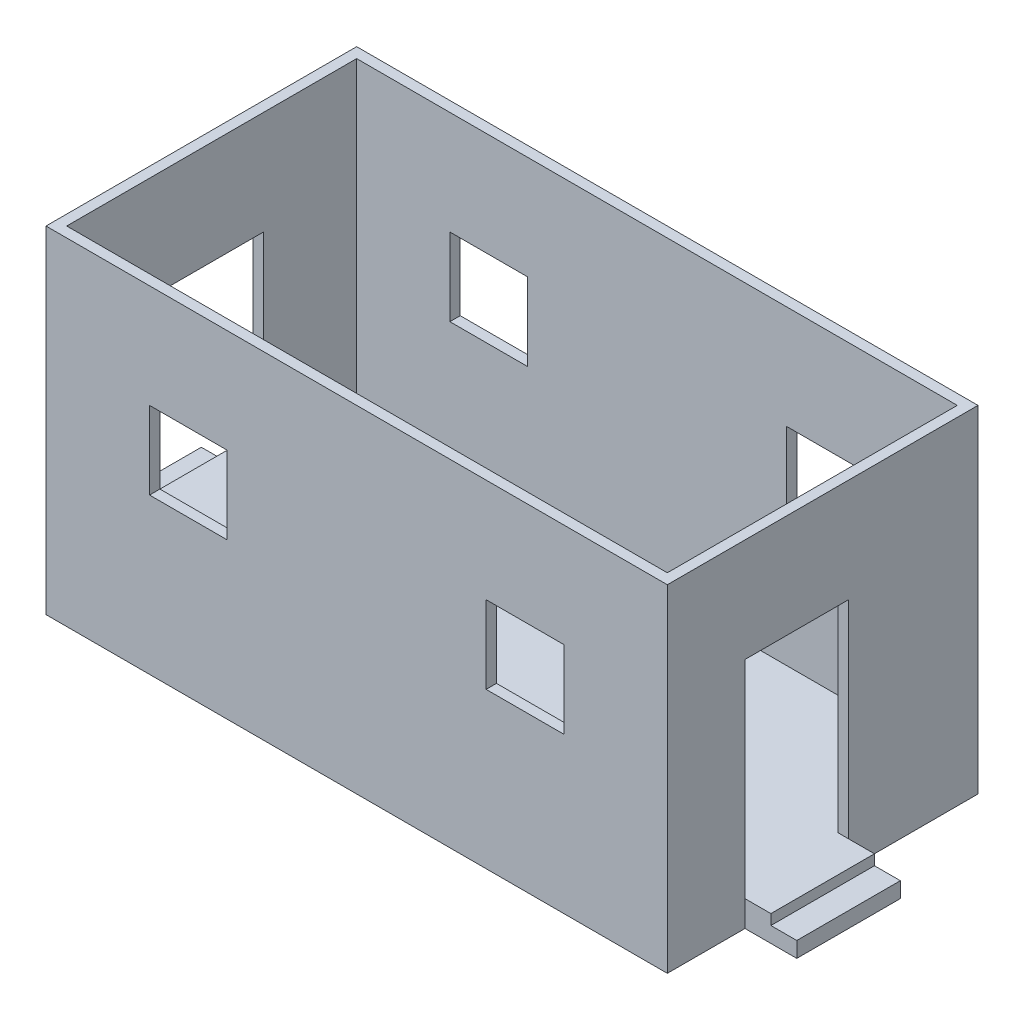
SolidWorks part; units mm, degrees
ref_plane "Front Plane" through (0, 0, 0) normal (0, 0, 1) x (1, 0, 0)
ref_plane "Top Plane" through (0, 0, 0) normal (0, 1, 0) x (1, 0, 0)
ref_plane "Right Plane" through (0, 0, 0) normal (1, 0, 0) x (0, 0, -1)
sketch "Sketch1" plane through (0, 0, 0) normal (0, 1, 0) x (1, 0, 0)
  line L1 (-3000, 1500) -> (3000, 1500)
  line L2 (-3000, 1500) -> (-3000, -1500)
  line L3 (-3000, -1500) -> (3000, -1500)
  line L4 (3000, 1500) -> (3000, -1500)
  line L5 (-3000, 1500) -> (3000, -1500) construction
  line L6 (-3000, -1500) -> (3000, 1500) construction
  point P0 (0, 0)
  dimension "D1" = 6000
  dimension "D2" = 3000
extrude "Boss-Extrude1" add sketch "Sketch1" along normal blind 250
sketch "Sketch2" plane through (0, 250, 0) normal (0, 1, 0) x (1, 0, 0)
  line L0 (-2900, 1400) -> (2900, 1400)
  line L1 (-3000, 1500) -> (3000, 1500)
  line L2 (-3000, 1500) -> (-3000, -1500)
  line L3 (-3000, -1500) -> (3000, -1500)
  line L4 (3000, 1500) -> (3000, -1500)
  line L5 (2900, 1400) -> (2900, -1400)
  line L6 (-2900, -1400) -> (2900, -1400)
  line L7 (-2900, 1400) -> (-2900, -1400)
  dimension "D1" = 100
extrude "Boss-Extrude2" add sketch "Sketch2" along normal blind 3000
sketch "Sketch3" plane through (-3000, 0, 0) normal (-1, 0, 0) x (0, 0, 1)
  line L0 (-1500, 0) -> (1500, 0) construction
  line L1 (-500, 2250) -> (500, 2250)
  line L2 (-500, 2250) -> (-500, 250)
  line L3 (-500, 250) -> (500, 250)
  line L4 (500, 2250) -> (500, 250)
  line L5 (1500, 3250) -> (1500, 0) construction
  dimension "D1" = 2000
  dimension "D2" = 250
  dimension "D3" = 1000
  dimension "D4" = 1000
extrude "Cut-Extrude1" cut sketch "Sketch3" against normal blind 250
sketch "Sketch4" plane through (3000, 0, 0) normal (1, 0, 0) x (0, 0, -1)
  line L0 (-1500, 0) -> (1500, 0) construction
  line L1 (-750, 2250) -> (250, 2250)
  line L2 (-750, 2250) -> (-750, 250)
  line L3 (-750, 250) -> (250, 250)
  line L4 (250, 2250) -> (250, 250)
  line L5 (-1500, 3250) -> (-1500, 0) construction
  dimension "D1" = 250
  dimension "D2" = 1000
  dimension "D3" = 2000
  dimension "D4" = 750
extrude "Cut-Extrude2" cut sketch "Sketch4" against normal blind 250
sketch "Sketch5" plane through (0, 0, 1500) normal (0, 0, 1) x (1, 0, 0)
  line L0 (-3000, 3250) -> (-3000, 0) construction
  line L1 (-2000, 2250) -> (-1250, 2250)
  line L2 (-2000, 2250) -> (-2000, 1500)
  line L3 (-2000, 1500) -> (-1250, 1500)
  line L4 (-1250, 2250) -> (-1250, 1500)
  line L5 (-3000, 0) -> (3000, 0) construction
  line L6 (3000, 3250) -> (3000, 0) construction
  line L7 (1250, 2250) -> (2000, 2250)
  line L8 (1250, 2250) -> (1250, 1500)
  line L9 (1250, 1500) -> (2000, 1500)
  line L10 (2000, 2250) -> (2000, 1500)
  dimension "D1" = 750
  dimension "D2" = 1000
  dimension "D3" = 1500
  dimension "D4" = 750
  dimension "D5" = 750
  dimension "D6" = 1000
  dimension "D7" = 1500
extrude "Cut-Extrude3" cut sketch "Sketch5" against normal through all
sketch "Sketch6" plane through (3000, 0, 0) normal (1, 0, 0) x (0, 0, -1)
  line L0 (-1500, 0) -> (1500, 0) construction
  line L1 (-750, 250) -> (250, 250)
  line L2 (-750, 250) -> (-750, 0)
  line L3 (-750, 0) -> (250, 0)
  line L4 (250, 250) -> (250, 0)
  dimension "D1" = 1000
extrude "Boss-Extrude4" add sketch "Sketch6" along normal blind 500
sketch "Sketch7" plane through (-3000, 0, 0) normal (-1, 0, 0) x (0, 0, 1)
  line L0 (-1500, 0) -> (1500, 0) construction
  line L1 (-500, 250) -> (500, 250)
  line L2 (-500, 250) -> (-500, 0)
  line L3 (-500, 0) -> (500, 0)
  line L4 (500, 250) -> (500, 0)
  dimension "D1" = 1000
extrude "Boss-Extrude5" add sketch "Sketch7" along normal blind 500
sketch "Sketch8" plane through (0, 250, 0) normal (0, 1, 0) x (1, 0, 0)
  line L0 (3500, -750) -> (3000, -750) construction
  line L1 (3500, 250) -> (3250, 250)
  line L2 (3500, 250) -> (3500, -750)
  line L3 (3500, -750) -> (3250, -750)
  line L4 (3250, 250) -> (3250, -750)
  dimension "D1" = 250
extrude "Cut-Extrude4" cut sketch "Sketch8" against normal blind 100
sketch "Sketch9" plane through (0, 250, 0) normal (0, 1, 0) x (1, 0, 0)
  line L0 (-3500, -500) -> (-3000, -500) construction
  line L1 (-3500, 500) -> (-3250, 500)
  line L2 (-3500, 500) -> (-3500, -500)
  line L3 (-3500, -500) -> (-3250, -500)
  line L4 (-3250, 500) -> (-3250, -500)
  dimension "D1" = 250
extrude "Cut-Extrude5" cut sketch "Sketch9" against normal blind 100
